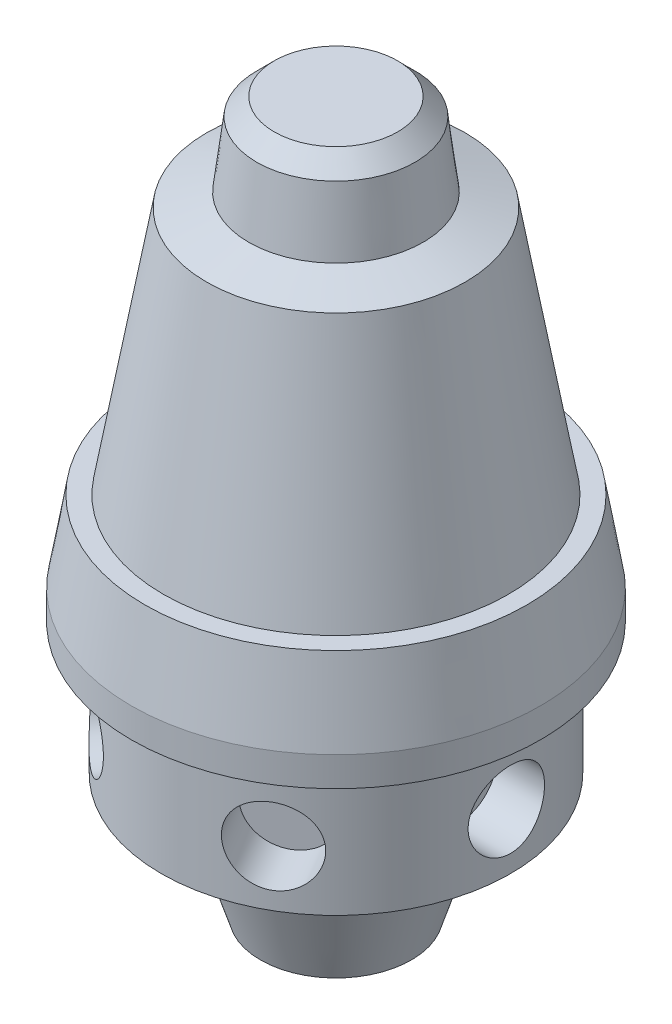
SolidWorks part; units mm, degrees
ref_plane "Спереди" through (0, 0, 0) normal (0, 0, 1) x (1, 0, 0)
ref_plane "Сверху" through (0, 0, 0) normal (0, 1, 0) x (1, 0, 0)
ref_plane "Справа" through (0, 0, 0) normal (1, 0, 0) x (0, 0, -1)
sketch "Эскиз1" plane through (0, 0, 0) normal (0, 0, 1) x (1, 0, 0)
  line L0 (0, 138.704) -> (0, -51.4576) construction
  line L1 (0, 0) -> (13.833, 0)
  line L2 (13.833, 0) -> (21.0933, 22.7793)
  line L3 (21.0933, 22.7793) -> (32, 22.7793)
  line L4 (32, 22.7793) -> (32, 46.7793)
  line L6 (0, 0) -> (0, 130.1556)
  line L7 (32, 46.7793) -> (37.5, 46.7793)
  line L9 (35, 66.9349) -> (37.5, 52.1747)
  line L10 (35, 66.9349) -> (31.6301, 66.9349)
  line L11 (31.6301, 66.9349) -> (23.7009, 112.524)
  line L12 (23.7009, 112.524) -> (15.9886, 114.9821)
  line L13 (15.9886, 114.9821) -> (14.5092, 126.9478)
  line L14 (14.5092, 126.9478) -> (11.3014, 130.1556)
  line L15 (11.3014, 130.1556) -> (0, 130.1556)
  line L16 (37.5, 52.1747) -> (37.5, 46.7793)
revolve "Повернуть1" add sketch "Эскиз1" angle 360 about L0
ref_plane "Плоскость1" through (-37.5, 0, 0) normal (-1, 0, 0) x (0, 1, 0)
ref_plane "Плоскость2" through (18.75, 0, 32.476) normal (0.5, 0, 0.866) x (0, 1, 0)
ref_plane "Плоскость3" through (-23.0873, 0, 29.5504) normal (-0.6157, 0, 0.788) x (0, 1, 0)
ref_plane "Плоскость4" through (37.5, 0, 0) normal (1, 0, 0) x (0, 1, 0)
sketch "Эскиз2" plane through (-37.5, 0, 0) normal (-1, 0, 0) x (0, 1, 0)
  line L0 (0, 0) -> (111.3593, 0) construction
  circle A0 centre (33, 0) radius 7
extrude "Вырез-Вытянуть1" cut sketch "Эскиз2" against normal blind 15
sketch "Эскиз3" plane through (18.75, 0, 32.476) normal (0.5, 0, 0.866) x (0, 1, 0)
  line L0 (0, 0) -> (46.7529, 0) construction
  circle A0 centre (33, 0) radius 7
extrude "Вырез-Вытянуть2" cut sketch "Эскиз3" against normal blind 15
sketch "Эскиз4" plane through (-23.0873, 0, 29.5504) normal (-0.6157, 0, 0.788) x (0, 1, 0)
  line L0 (0, 0) -> (43.6527, 0) construction
  circle A0 centre (33, 0) radius 7
extrude "Вырез-Вытянуть3" cut sketch "Эскиз4" against normal blind 15
sketch "Эскиз5" plane through (37.5, 0, 0) normal (1, 0, 0) x (0, 1, 0)
  line L0 (0, 0) -> (43.6527, 0) construction
  circle A0 centre (33, 0) radius 7
extrude "Вырез-Вытянуть4" cut sketch "Эскиз5" against normal blind 15
